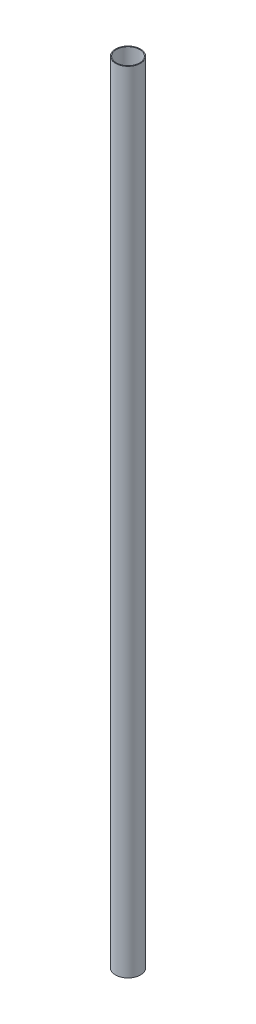
SolidWorks part; units mm, degrees
ref_plane "Plan de face" through (0, 0, 0) normal (0, 0, 1) x (1, 0, 0)
ref_plane "Plan de dessus" through (0, 0, 0) normal (0, 1, 0) x (1, 0, 0)
ref_plane "Plan de droite" through (0, 0, 0) normal (1, 0, 0) x (0, 0, -1)
sketch "Esquisse1" plane through (0, 0, 0) normal (0, 1, 0) x (1, 0, 0)
  circle A0 centre (0, 0) radius 15
  circle A1 centre (0, 0) radius 14
  dimension "D1" = 1
extrude "Boss.-Extru.1" add sketch "Esquisse1" along normal blind 950
